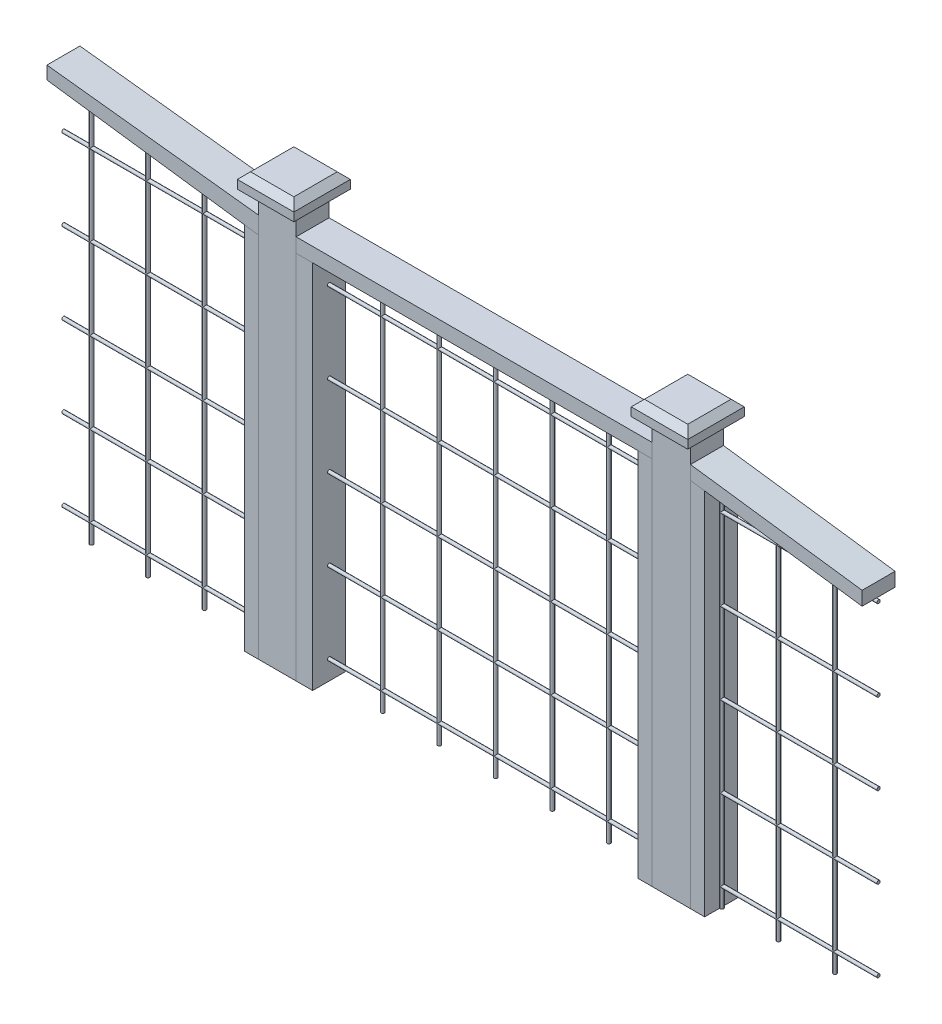
SolidWorks part; units mm, degrees
material "Cedar"
ref_plane "Front Plane" through (0, 0, 0) normal (0, 0, 1) x (1, 0, 0)
ref_plane "Top Plane" through (0, 0, 0) normal (0, 1, 0) x (1, 0, 0)
ref_plane "Right Plane" through (0, 0, 0) normal (1, 0, 0) x (0, 0, -1)
sketch "Picture" plane through (0, 0, 0) normal (0, 0, 1) x (1, 0, 0)
  line L0 (584.7238, 841.0986) -> (673.6238, 841.0986) construction
  dimension "D1" = 88.9
sketch "Sketch2" plane through (0, 0, 0) normal (0, 0, 1) x (1, 0, 0)
  line L0 (671.6637, 1172.0123) -> (570.8872, 1172.0123)
  line L1 (1735.1055, 1172.0123) -> (1631.6146, 1172.0123)
  line L2 (1735.1055, 1172.0123) -> (1735.1055, 0)
  line L3 (1735.1055, 0) -> (1631.6146, 0)
  line L4 (1631.6146, 1172.0123) -> (1631.6146, 0)
  line L5 (570.8872, 1172.0123) -> (570.8872, 0)
  line L7 (671.6637, 0) -> (671.6637, 1172.0123)
  line L8 (570.8872, 0) -> (671.6637, 0)
extrude "Posts" add sketch "Sketch2" along normal mid plane 88.9
sketch "Sketch3" plane through (0, 0, 0) normal (0, 0, 1) x (1, 0, 0)
  line L0 (570.8872, 1037.1452) -> (0, 1102.3724)
  line L1 (570.8872, 1172.0123) -> (570.8872, 0) construction
  line L2 (0, 1102.3724) -> (0, 1067.4254)
  line L3 (0, 1067.4254) -> (570.8872, 990.6073)
  line L4 (570.8872, 990.6073) -> (570.8872, 1037.1452)
  line L5 (1735.1055, 1037.1452) -> (2197.8523, 974.8783)
  line L6 (1735.1055, 0) -> (1735.1055, 1172.0123) construction
  line L7 (2197.8523, 974.8783) -> (2197.8523, 937.5698)
  line L8 (2197.8523, 937.5698) -> (1735.1055, 999.8367)
  line L9 (1735.1055, 999.8367) -> (1735.1055, 1037.1452)
extrude "Top 2x4" add sketch "Sketch3" along normal mid plane 88.9 separate body
sketch "Sketch4" plane through (0, 0, 0) normal (0, 0, 1) x (1, 0, 0)
  line L0 (532.978, 995.7083) -> (532.978, 0)
  line L1 (0, 1067.4254) -> (570.8872, 990.6073) construction
  line L2 (532.978, 0) -> (570.8872, 0)
  line L3 (570.8872, 1172.0123) -> (570.8872, 0) construction
  line L4 (570.8872, 0) -> (570.8872, 990.6073)
  line L5 (570.8872, 990.6073) -> (532.978, 995.7083)
  line L6 (1735.1055, 0) -> (1773.3725, 0)
  line L7 (1773.3725, 0) -> (1773.3725, 994.6875)
  line L8 (1735.1055, 999.8367) -> (2197.8523, 937.5698) construction
  line L9 (1773.3725, 994.6875) -> (1735.1055, 999.8367)
  line L10 (1735.1055, 999.8367) -> (1735.1055, 0)
extrude "Side Verticals" add sketch "Sketch4" along normal mid plane 88.9 separate body
sketch "Sketch5" plane through (0, 0, 0) normal (0, 0, 1) x (1, 0, 0)
  line L0 (671.8949, 1037.1452) -> (1630.9475, 1037.1452)
  line L1 (671.8949, 1037.1452) -> (671.8949, 998.8396)
  line L2 (671.8949, 998.8396) -> (1630.9475, 998.8396)
  line L3 (1630.9475, 998.8396) -> (1630.9475, 1037.1452)
  point P0 (570.8872, 1037.1452)
extrude "Gate Frame Top" add sketch "Sketch5" along normal mid plane 88.9 separate body
sketch "Sketch7" plane through (0, 0, 0) normal (0, 0, 1) x (1, 0, 0)
  line L0 (671.8949, 998.8396) -> (716.4365, 998.8396)
  line L1 (671.8949, 998.8396) -> (1630.9475, 998.8396) construction
  line L2 (671.8949, 998.8396) -> (671.6637, 0)
  line L3 (671.6637, 0) -> (671.6637, 1172.0123) construction
  line L4 (671.6637, 0) -> (716.4365, 0)
  line L5 (716.4365, 0) -> (716.4365, 998.8396)
  line L6 (1630.9475, 998.8396) -> (1631.6146, 0)
  line L7 (1631.6146, 0) -> (1593.3347, 0)
  line L8 (1593.3347, 0) -> (1593.3347, 998.8396)
  line L9 (1593.3347, 998.8396) -> (1630.9475, 998.8396)
extrude "Gate Side Verticals" add sketch "Sketch7" along normal mid plane 88.9 separate body
sketch "Sketch9" plane through (0, 998.8396, 0) normal (0, -1, 0) x (-1, 0, 0)
  line L2 (-716.4365, -44.45) -> (-716.4365, 44.45) construction
  circle A0 centre (-861.2165, 0) radius 4.5105
  circle A1 centre (-1013.6165, 0) radius 4.5105
  circle A2 centre (-1166.0165, 0) radius 4.5105
  circle A3 centre (-1318.4165, 0) radius 4.5105
  circle A4 centre (-1470.8165, 0) radius 4.5105
  circle A5 centre (-1623.2165, 0) radius 4.5105
  circle A6 centre (-1775.6165, 0) radius 4.5105
  circle A7 centre (-1928.0165, 0) radius 4.5105
  circle A8 centre (-2080.4165, 0) radius 4.5105
  dimension "D1" = 9
  dimension "D2" = 144.78
extrude "Gate and Right Vert Wire" add sketch "Sketch9" along normal up to surface (998.8396 mm away) separate body up to face at (694.0501, 0, 0)
sketch "Sketch11" plane through (0, 998.8396, 0) normal (0, -1, 0) x (1, 0, 0)
  line L0 (532.978, 44.45) -> (532.978, -44.45) construction
  circle A0 centre (380.578, 0) radius 4.5322
  circle A1 centre (228.178, 0) radius 4.5322
  circle A2 centre (75.778, 0) radius 4.5322
  dimension "D1" = 152.4
  dimension "D2" = 3
extrude "Left Vert Wire" add sketch "Sketch11" against normal up to surface and the other way up to surface (998.8396 mm away) separate body up to face at (285.4436, 1029.0163, 0) other way up to face at (551.9326, 0, 0)
sketch "Sketch12" plane through (532.978, 0, 0) normal (-1, 0, 0) x (0, 0, 1)
  circle A0 centre (0, 926.0732) radius 4.4474
  circle A1 centre (0, 707.6332) radius 4.4474
  circle A2 centre (0, 489.1932) radius 4.4474
  circle A3 centre (0, 270.7532) radius 4.4474
  circle A4 centre (0, 52.3132) radius 4.4474
  point P0 (0, 926.0732)
  dimension "D1" = 5
extrude "Horizontal Wire" add sketch "Sketch12" along normal up to surface and the other way up to surface separate body
sketch "Sketch13" plane through (0, 998.8396, 0) normal (0, 1, 0) x (1, 0, 0)
  circle A0 centre (2080.4165, 0) radius 4.5105
extrude "Cut-Extrude1" cut sketch "Sketch13" against normal blind 21.336
sketch "Sketch14" plane through (0, 1172.0123, 0) normal (0, 1, 0) x (1, 0, 0)
  line L0 (1735.1055, -44.45) -> (1631.6146, -44.45) construction
  line L1 (1735.1055, -44.45) -> (1735.1055, 44.45) construction
  line L2 (1631.6146, -44.45) -> (1631.6146, 44.45) construction
  line L3 (1735.1055, 44.45) -> (1631.6146, 44.45) construction
  line L4 (671.6637, 44.45) -> (570.8872, 44.45) construction
  line L5 (570.8872, -44.45) -> (570.8872, 44.45) construction
  line L6 (671.6637, -44.45) -> (671.6637, 44.45) construction
  line L7 (671.6637, -44.45) -> (570.8872, -44.45) construction
  line L8 (1735.1055, -44.45) -> (1631.6146, -44.45)
  line L9 (1735.1055, -44.45) -> (1735.1055, 44.45)
  line L10 (1631.6146, -44.45) -> (1631.6146, 44.45)
  line L11 (1735.1055, 44.45) -> (1631.6146, 44.45)
  line L12 (671.6637, 44.45) -> (570.8872, 44.45)
  line L13 (570.8872, -44.45) -> (570.8872, 44.45)
  line L14 (671.6637, -44.45) -> (671.6637, 44.45)
  line L15 (671.6637, -44.45) -> (570.8872, -44.45)
extrude "Cut-Extrude2" cut sketch "Sketch14" against normal blind 71.12
sketch "Sketch15" plane through (0, 0, 0) normal (0, 0, 1) x (1, 0, 0)
  line L0 (1631.6146, 1100.8923) -> (1631.6146, 0) construction
  line L1 (671.6637, 1100.8923) -> (1631.6146, 1100.8923)
  line L2 (671.6637, 1100.8923) -> (671.6637, 1062.7923)
  line L3 (671.6637, 1062.7923) -> (1631.6146, 1062.7923)
  line L4 (1631.6146, 1100.8923) -> (1631.6146, 1062.7923)
  dimension "D1" = 38.1
extrude "Gate Bottom Piece" [suppressed] add sketch "Sketch15" along normal mid plane 88.9 separate body
sketch "Sketch16" [suppressed] plane through (0, 0, 0) normal (0, 0, 1) x (1, 0, 0)
  line L0 (1630.9475, 1037.1452) -> (671.8949, 1037.1452) construction
  line L5 (440.2212, 1138.9923) -> (1862.6212, 1138.9923)
  line L6 (440.2212, 1138.9923) -> (440.2212, 1100.8923)
  line L7 (440.2212, 1100.8923) -> (1862.6212, 1100.8923)
  line L8 (1862.6212, 1138.9923) -> (1862.6212, 1100.8923)
  line L9 (440.2212, 1138.9923) -> (1862.6212, 1100.8923) construction
  line L10 (440.2212, 1100.8923) -> (1862.6212, 1138.9923) construction
  line L11 (1631.6146, 1100.8923) -> (671.6637, 1100.8923) construction
  point P0 (1151.4212, 1119.9423)
  point P5 (1151.4212, 1037.1452)
  dimension "D1" = 38.1
  dimension "D2" = 1422.4
extrude "Gate Middle Piece" [suppressed] add sketch "Sketch16" along normal mid plane 139.7 separate body
chamfer "L Chamfer1" [suppressed] distance 88.9 distance2 63.5
chamfer "R Chamfer1" [suppressed] distance 63.5 distance2 88.9
sketch "Sketch20" [suppressed] plane through (0, 0, 0) normal (0, 0, 1) x (1, 0, 0)
  line L1 (440.2212, 1177.0923) -> (1862.6212, 1177.0923)
  line L2 (440.2212, 1177.0923) -> (440.2212, 1138.9923)
  line L3 (440.2212, 1138.9923) -> (1862.6212, 1138.9923)
  line L4 (1862.6212, 1177.0923) -> (1862.6212, 1138.9923)
  line L5 (440.2212, 1177.0923) -> (1862.6212, 1138.9923) construction
  line L6 (440.2212, 1138.9923) -> (1862.6212, 1177.0923) construction
  point P0 (1151.4212, 1158.0423)
  dimension "D1" = 38.1
extrude "Above 1st" [suppressed] add sketch "Sketch20" along normal mid plane 139.7 separate body
chamfer "L Chamfer2" [suppressed] distance 50.8 angle 35.5
chamfer "R Chamfer2" [suppressed] distance 36.322 angle 54.5
sketch "Sketch17" [suppressed] plane through (0, 1785.4496, 0) normal (0, 0, 1) x (1, 0, 0)
  line L1 (569.3121, -570.5823) -> (1733.5303, -570.5823)
  line L2 (569.3121, -570.5823) -> (569.3121, -608.6823)
  line L3 (569.3121, -608.6823) -> (1733.5303, -608.6823)
  line L4 (1733.5303, -570.5823) -> (1733.5303, -608.6823)
  line L5 (569.3121, -570.5823) -> (1733.5303, -608.6823) construction
  line L6 (569.3121, -608.6823) -> (1733.5303, -570.5823) construction
  point P0 (1151.4212, -589.6323)
  dimension "D1" = 38.1
extrude "Gate Top Piece" [suppressed] add sketch "Sketch17" along normal mid plane 88.9 separate body
chamfer "L Chamfer2-1" [suppressed] distance 22.86 angle 59.04
chamfer "R Chamfer2-1" [suppressed] distance 38.1 angle 30.96
sketch "Sketch21" [suppressed] plane through (0, 203.177, 0) normal (0, 0, 1) x (1, 0, 0)
  line L1 (567.6502, 1049.7903) -> (1735.1055, 1049.7903)
  line L2 (567.6502, 1049.7903) -> (567.6502, 1011.6903)
  line L3 (567.6502, 1011.6903) -> (1735.1055, 1011.6903)
  line L4 (1735.1055, 1049.7903) -> (1735.1055, 1011.6903)
  line L5 (567.6502, 1049.7903) -> (1735.1055, 1011.6903) construction
  line L6 (567.6502, 1011.6903) -> (1735.1055, 1049.7903) construction
  line L8 (569.3121, 1011.6903) -> (1733.5303, 1011.6903) construction
  point P0 (1151.3778, 1030.7403)
  dimension "D1" = 38.1
extrude "Above 1st-2" [suppressed] add sketch "Sketch21" along normal mid plane 88.9 separate body
chamfer "L Chamfer2-2" [suppressed] distance 47.371 angle 59.04
chamfer "R Chamfer2-2" [suppressed] distance 78.74 angle 30.96
sketch "Sketch23" plane through (0, 1100.8923, 0) normal (0, 1, 0) x (1, 0, 0)
  line L5 (1607.16, -76.2) -> (1759.56, -76.2)
  line L6 (1607.16, -76.2) -> (1607.16, 76.2)
  line L11 (1607.16, 76.2) -> (1759.56, 76.2)
  line L12 (1759.56, -76.2) -> (1759.56, 76.2)
  line L13 (1607.16, -76.2) -> (1759.56, 76.2) construction
  line L14 (1607.16, 76.2) -> (1759.56, -76.2) construction
  line L15 (545.0755, -76.2) -> (697.4755, -76.2)
  line L16 (545.0755, -76.2) -> (545.0755, 76.2)
  line L17 (545.0755, 76.2) -> (697.4755, 76.2)
  line L18 (697.4755, -76.2) -> (697.4755, 76.2)
  line L19 (545.0755, -76.2) -> (697.4755, 76.2) construction
  line L20 (545.0755, 76.2) -> (697.4755, -76.2) construction
  point P0 (1683.36, 0)
  point P1 (621.2755, 0)
  point P2 (1683.36, 0)
  point P10 (621.2755, 0)
  point P11 (1683.36, 0)
  point P12 (1683.36, 0)
  dimension "D1" = 152.4
  dimension "D2" = 152.4
  dimension "D3" = 152.4
  dimension "D4" = 152.4
extrude "Boss-Extrude1" add sketch "Sketch23" along normal blind 40.64 separate body
chamfer "Chamfer1" distance 17.78 angle 45 4 edges at (621.2755, 1141.5323, 76.2) (545.0755, 1141.5323, 0) (621.2755, 1141.5323, -76.2) (697.4755, 1141.5323, 0)
chamfer "Chamfer2" distance 17.78 angle 45 4 edges at (1683.36, 1141.5323, 76.2) (1607.16, 1141.5323, 0) (1683.36, 1141.5323, -76.2) (1759.56, 1141.5323, 0)
